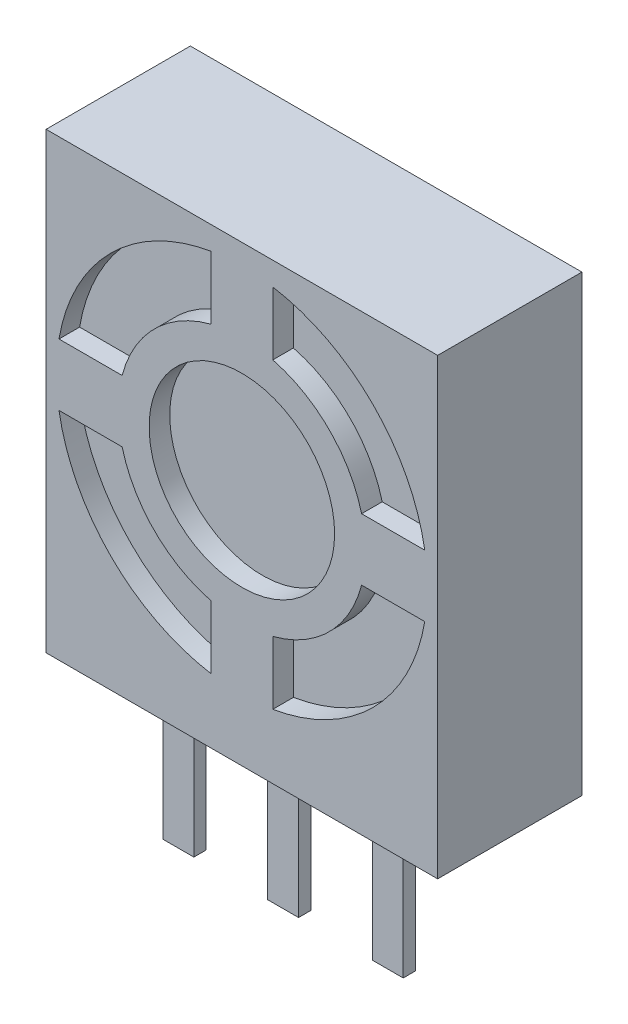
SolidWorks part; units mm, degrees
ref_plane "정면" through (0, 0, 0) normal (0, 0, 1) x (1, 0, 0)
ref_plane "윗면" through (0, 0, 0) normal (0, 1, 0) x (1, 0, 0)
ref_plane "우측면" through (0, 0, 0) normal (1, 0, 0) x (0, 0, -1)
sketch "스케치1" plane through (0, 0, 0) normal (0, 0, 1) x (1, 0, 0)
  line L1 (-4.75, -5.5) -> (4.75, -5.5)
  line L2 (-4.75, -5.5) -> (-4.75, 5.5)
  line L3 (-4.75, 5.5) -> (4.75, 5.5)
  line L4 (4.75, -5.5) -> (4.75, 5.5)
  line L5 (-4.75, -5.5) -> (4.75, 5.5) construction
  line L6 (-4.75, 5.5) -> (4.75, -5.5) construction
  point P0 (0, 0)
extrude "보스-돌출1" add sketch "스케치1" along normal blind 3.5
sketch "스케치2" plane through (0, 0, 3.5) normal (0, 0, 1) x (1, 0, 0)
  line L0 (4.75, 5.5) -> (-4.75, 5.5) construction
  line L1 (0.75, 4.9371) -> (0.75, 3.4047)
  line L2 (-0.75, 1.25) -> (0.75, 1.25) construction
  line L3 (-0.75, 1.25) -> (-0.75, -0.25) construction
  line L4 (-0.75, -0.25) -> (0.75, -0.25) construction
  line L5 (0.75, 1.25) -> (0.75, -0.25) construction
  line L6 (-0.75, 1.25) -> (0.75, -0.25) construction
  line L7 (-0.75, -0.25) -> (0.75, 1.25) construction
  line L8 (-0.75, 4.9371) -> (-0.75, 3.4047)
  line L9 (-4.4371, 1.25) -> (-2.9047, 1.25)
  line L10 (-4.4371, -0.25) -> (-2.9047, -0.25)
  line L13 (-0.75, -2.4047) -> (-0.75, -3.9371)
  line L14 (0.75, -2.4047) -> (0.75, -3.9371)
  line L15 (2.9047, -0.25) -> (4.4371, -0.25)
  line L16 (2.9047, 1.25) -> (4.4371, 1.25)
  arc A0 (-4.4371, -0.25) -> (-0.75, -3.9371) centre (0, 0.5) ccw
  arc A1 (-2.9047, -0.25) -> (-0.75, -2.4047) centre (0, 0.5) ccw
  arc A2 (2.9047, 1.25) -> (0.75, 3.4047) centre (0, 0.5) ccw
  arc A3 (4.4371, 1.25) -> (0.75, 4.9371) centre (0, 0.5) ccw
  arc A4 (-0.75, 4.9371) -> (-4.4371, 1.25) centre (0, 0.5) ccw
  arc A5 (-0.75, 3.4047) -> (-2.9047, 1.25) centre (0, 0.5) ccw
  arc A6 (0.75, -2.4047) -> (2.9047, -0.25) centre (0, 0.5) ccw
  arc A7 (0.75, -3.9371) -> (4.4371, -0.25) centre (0, 0.5) ccw
  circle A8 centre (0, 0.5) radius 2.25
  point P12 (0.75, 0.5)
  point P15 (-0.75, 0.5)
  point P18 (0, 1.25)
  point P21 (0, -0.25)
  dimension "D1" = 5
extrude "컷-돌출1" cut sketch "스케치2" against normal blind 0.5
sketch "스케치4" plane through (0, -5.5, 0) normal (0, -1, 0) x (1, 0, 0)
  line L0 (-4.75, 2.5) -> (4.75, 2.5) construction
  line L1 (-4.75, 3.5) -> (-4.75, 0) construction
  line L2 (4.75, 3.5) -> (4.75, 0) construction
  line L3 (-4.75, 3.5) -> (4.75, 3.5) construction
  line L4 (0, 0) -> (0, 3.5) construction
  line L5 (-0.375, 2.2) -> (0.375, 2.2)
  line L6 (-0.375, 2.2) -> (-0.375, 2.5)
  line L7 (-0.375, 2.5) -> (0.375, 2.5)
  line L8 (0.375, 2.2) -> (0.375, 2.5)
  point P16 (0, 2.2)
  dimension "D1" = 1
  dimension "D2" = 0.75
  dimension "D3" = 0.3
extrude "보스-돌출2" add sketch "스케치4" along normal blind 3.5 separate body
pattern_linear "선형 패턴1" count 2 spacing 2.54 along (-1, 0, 0) count 2 spacing 2.54 along (1, 0, 0) of "보스-돌출2"
ref_plane "평면1" through (0, 0, 0) normal (1, 0, 0) x (0, 0, -1)
